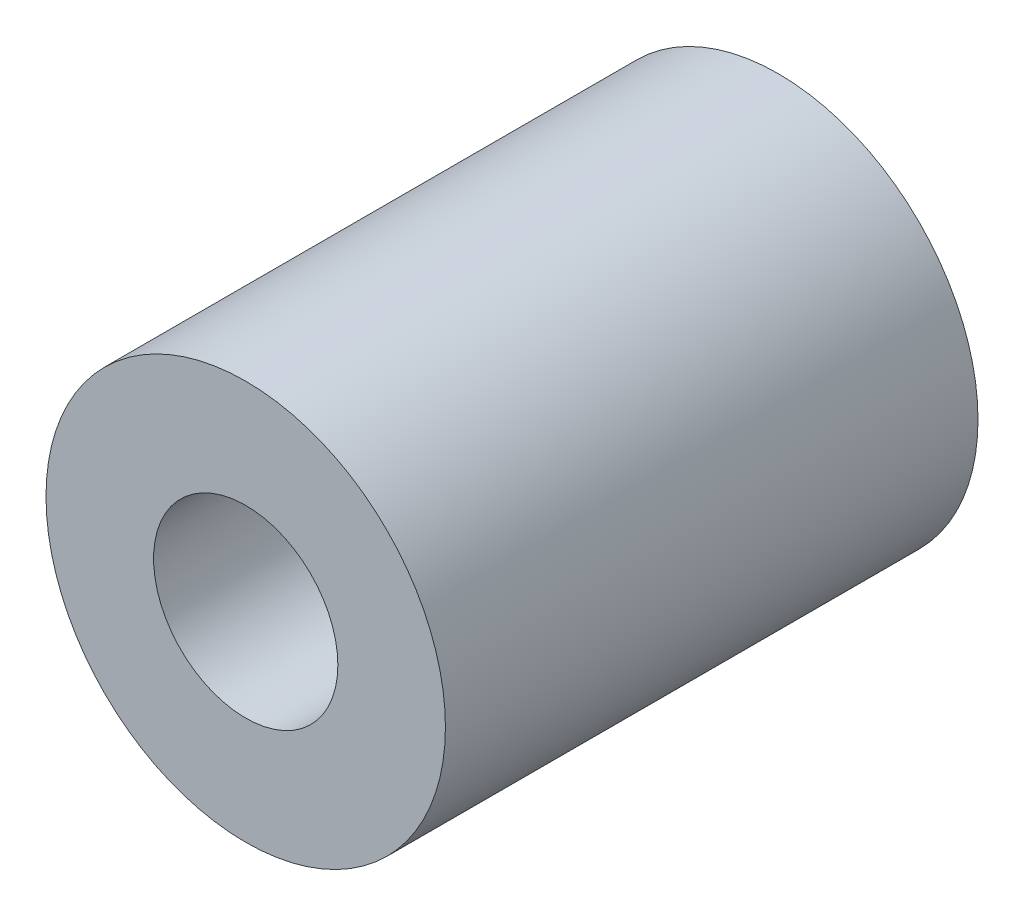
SolidWorks part; units mm, degrees
material "Nylon 6/10"
ref_plane "Front Plane" through (0, 0, 0) normal (0, 0, 1) x (1, 0, 0)
ref_plane "Top Plane" through (0, 0, 0) normal (0, 1, 0) x (1, 0, 0)
ref_plane "Right Plane" through (0, 0, 0) normal (1, 0, 0) x (0, 0, -1)
sketch "Sketch1" plane through (0, 0, 0) normal (0, 0, 1) x (1, 0, 0)
  circle A0 centre (0, 0) radius 2.1971
  circle A1 centre (0, 0) radius 4.7625
  dimension "D1" = 4.3942
  dimension "D2" = 9.525
extrude "Boss-Extrude1" add sketch "Sketch1" along normal mid plane 12.7
sketch "Sketch2" plane through (0, 0, 0) normal (0, 1, 0) x (1, 0, 0)
  circle A0 centre (0, 0) radius 1.25
  dimension "D1" = 2.5
extrude "Cut-Extrude1" cut sketch "Sketch2" against normal through all
